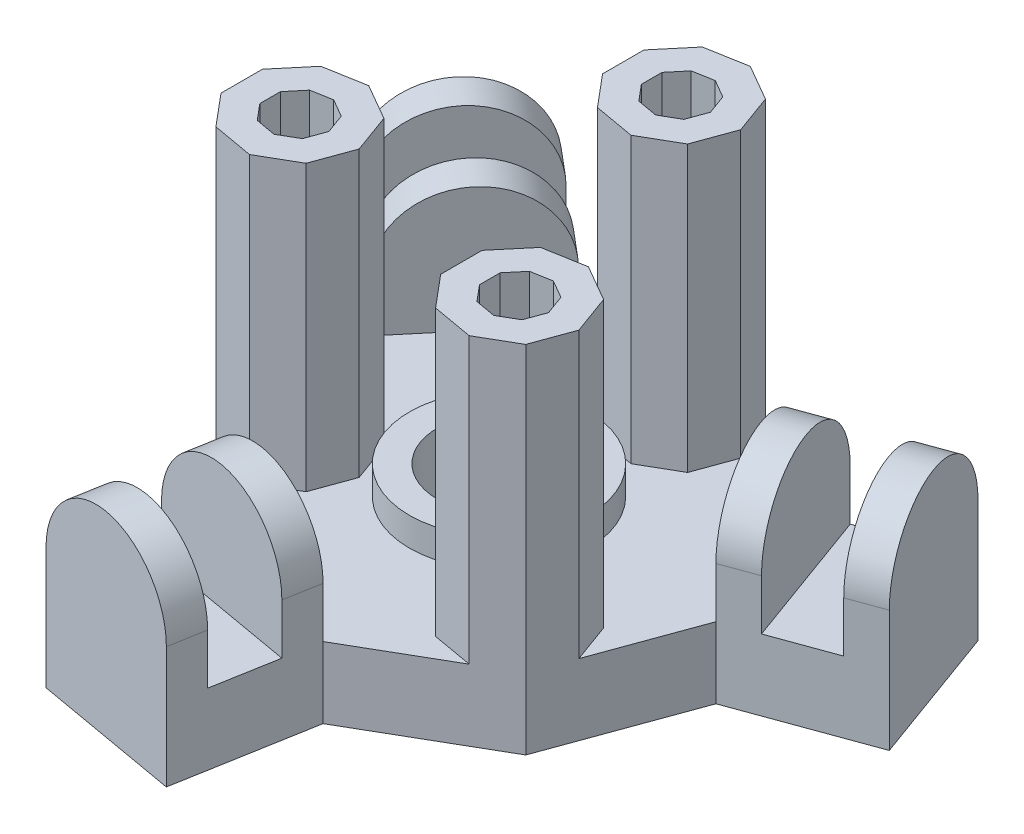
SolidWorks part; units mm, degrees
ref_plane "Front Plane" through (0, 0, 0) normal (0, 0, 1) x (1, 0, 0)
ref_plane "Top Plane" through (0, 0, 0) normal (0, 1, 0) x (1, 0, 0)
ref_plane "Right Plane" through (0, 0, 0) normal (1, 0, 0) x (0, 0, -1)
sketch "Sketch1" plane through (0, 0, 0) normal (0, 1, 0) x (1, 0, 0)
  line L0 (-18.2, -6.6243) -> (-9.684, -16.7732)
  line L1 (14.8368, -12.4495) -> (19.368, 0)
  line L2 (19.368, 0) -> (14.8368, 12.4495)
  line L3 (14.8368, 12.4495) -> (3.3632, 19.0738)
  line L4 (3.3632, 19.0738) -> (-9.684, 16.7732)
  line L5 (-9.684, 16.7732) -> (-18.2, 6.6243)
  line L6 (-18.2, 6.6243) -> (-18.2, -6.6243)
  line L7 (-9.684, -16.7732) -> (3.3632, -19.0738)
  line L8 (3.3632, -19.0738) -> (14.8368, -12.4495)
  line L9 (14.8368, 12.4495) -> (19.368, 0)
  line L10 (14.8368, 12.4495) -> (26.1868, 16.5806)
  line L11 (19.368, 0) -> (30.718, 4.1311)
  line L12 (26.1868, 16.5806) -> (30.718, 4.1311)
  line L13 (3.3632, -19.0738) -> (-9.684, -16.7732)
  line L14 (3.3632, -19.0738) -> (1.2658, -30.9687)
  line L15 (-9.684, -16.7732) -> (-11.7814, -28.6681)
  line L16 (1.2658, -30.9687) -> (-11.7814, -28.6681)
  line L17 (-18.2, 6.6243) -> (-9.684, 16.7732)
  line L18 (-18.2, 6.6243) -> (-27.4526, 14.3881)
  line L19 (-9.684, 16.7732) -> (-18.9366, 24.5371)
  line L20 (-27.4526, 14.3881) -> (-18.9366, 24.5371)
  circle A0 centre (0, 0) radius 18.2 construction
  circle A1 centre (0, 0) radius 5.5
  dimension "D1" = 36.4
  dimension "D2" = 11
  dimension "D3" = 11.35
extrude "Boss-Extrude1" add sketch "Sketch1" along normal blind 6.35 contours L16 L14 L7 L15 | L7 L8 L1 L2 L3 L4 L5 L6 L0 A1 | L12 L10 L2 L11 | L20 L18 L5 L19
ref_plane "Plane1" through (-5.2578, 0, 29.8184) normal (0.1736, 0, -0.9848) x (-0.9848, 0, -0.1736)
sketch "Sketch4" plane through (-5.2578, 0, 29.8184) normal (0.1736, 0, -0.9848) x (-0.9848, 0, -0.1736)
  line L0 (-6.6243, 6.35) -> (-6.6243, 10.85)
  line L1 (6.6243, 6.35) -> (6.6243, 10.85)
  line L2 (-6.6243, 6.35) -> (6.6243, 6.35)
  arc A0 (6.6243, 10.85) -> (-6.6243, 10.85) centre (0, 10.85) ccw
  dimension "D1" = 4.5
extrude "Boss-Extrude2" add sketch "Sketch4" along normal blind 3.18
ref_plane "Plane2" through (-3.1604, 0, 17.9235) normal (0.1736, 0, -0.9848) x (-0.9848, 0, -0.1736)
sketch "Sketch6" plane through (-3.1604, 0, 17.9235) normal (0.1736, 0, -0.9848) x (-0.9848, 0, -0.1736)
  line L0 (-6.6243, 6.35) -> (-6.6243, 10.85)
  line L1 (6.6243, 6.35) -> (6.6243, 10.85)
  line L2 (-6.6243, 6.35) -> (6.6243, 6.35)
  arc A0 (6.6243, 10.85) -> (-6.6243, 10.85) centre (0, 10.85) ccw
  dimension "D1" = 4.5
extrude "Boss-Extrude4" add sketch "Sketch6" against normal blind 3.175
ref_plane "Plane3" through (28.4524, 0, -10.3558) normal (-0.9397, 0, 0.342) x (0.342, 0, 0.9397)
sketch "Sketch8" plane through (28.4524, 0, -10.3558) normal (-0.9397, 0, 0.342) x (0.342, 0, 0.9397)
  line L0 (-6.6243, 10.85) -> (-6.6243, 6.35)
  line L1 (-6.6243, 6.35) -> (6.6243, 6.35)
  line L2 (6.6243, 6.35) -> (6.6243, 10.85)
  arc A0 (6.6243, 10.85) -> (-6.6243, 10.85) centre (0, 10.85) ccw
  dimension "D1" = 4.5
extrude "Boss-Extrude5" add sketch "Sketch8" along normal blind 3.175
ref_plane "Plane4" through (17.1024, 0, -6.2248) normal (-0.9397, 0, 0.342) x (0.342, 0, 0.9397)
sketch "Sketch9" plane through (17.1024, 0, -6.2248) normal (-0.9397, 0, 0.342) x (0.342, 0, 0.9397)
  line L0 (-6.6243, 6.35) -> (-6.6243, 10.85)
  line L1 (-6.6243, 6.35) -> (6.6243, 6.35)
  line L2 (6.6243, 6.35) -> (6.6243, 10.85)
  arc A0 (-6.6243, 10.85) -> (6.6243, 10.85) centre (0, 10.85) cw
  dimension "D1" = 4.5
extrude "Boss-Extrude6" add sketch "Sketch9" against normal blind 3.175
ref_plane "Plane5" through (-23.1946, 0, -19.4626) normal (0.766, 0, 0.6428) x (0.6428, 0, -0.766)
sketch "Sketch10" plane through (-23.1946, 0, -19.4626) normal (0.766, 0, 0.6428) x (0.6428, 0, -0.766)
  line L0 (-6.6243, 10.85) -> (-6.6243, 6.35)
  line L1 (-6.6243, 6.35) -> (6.6243, 6.35)
  line L2 (6.6243, 6.35) -> (6.6243, 10.85)
  arc A0 (6.6243, 10.85) -> (-6.6243, 10.85) centre (0, 10.85) ccw
  dimension "D1" = 4.5
extrude "Boss-Extrude7" add sketch "Sketch10" along normal blind 3.175
ref_plane "Plane6" through (-13.942, 0, -11.6987) normal (0.766, 0, 0.6428) x (0.6428, 0, -0.766)
sketch "Sketch11" plane through (-13.942, 0, -11.6987) normal (0.766, 0, 0.6428) x (0.6428, 0, -0.766)
  line L0 (-6.6243, 10.85) -> (-6.6243, 6.35)
  line L1 (-6.6243, 6.35) -> (6.6243, 6.35)
  line L2 (6.6243, 6.35) -> (6.6243, 10.85)
  arc A0 (6.6243, 10.85) -> (-6.6243, 10.85) centre (0, 10.85) ccw
  dimension "D1" = 4.5
extrude "Boss-Extrude8" add sketch "Sketch11" against normal blind 3.175
ref_plane "Plane7" through (0, 6.35, 0) normal (0, 1, 0) x (1, 0, 0)
sketch "Sketch12" plane through (0, 6.35, 0) normal (0, 1, 0) x (1, 0, 0)
  line L9 (14.8368, -12.4495) -> (19.368, 0) construction
  line L29 (14.8368, -12.4495) -> (16.1015, -8.9746)
  line L38 (16.1015, -8.9746) -> (14.8368, -5.4997)
  line L48 (6.5657, 10.275) -> (7.8305, 13.7499)
  line L49 (3.3632, 19.0738) -> (-0.2785, 18.4317)
  line L50 (-0.2785, 18.4317) -> (-2.6555, 15.5989)
  line L51 (-2.6555, 15.5989) -> (-2.6555, 11.9009)
  line L52 (-2.6555, 11.9009) -> (-0.2785, 9.0681)
  line L53 (-0.2785, 9.0681) -> (3.3632, 8.426)
  line L54 (3.3632, 8.426) -> (6.5657, 10.275)
  line L55 (7.8305, 13.7499) -> (6.5657, 17.2248)
  line L56 (6.5657, 17.2248) -> (3.3632, 19.0738)
  line L57 (14.8368, -5.4997) -> (11.6343, -3.6507)
  line L58 (11.6343, -3.6507) -> (7.9925, -4.2929)
  line L59 (7.9925, -4.2929) -> (5.6155, -7.1256)
  line L60 (5.6155, -7.1256) -> (5.6155, -10.8236)
  line L61 (5.6155, -10.8236) -> (7.9925, -13.6564)
  line L62 (7.9925, -13.6564) -> (11.6343, -14.2985)
  line L63 (11.6343, -14.2985) -> (14.8368, -12.4495)
  line L64 (-18.2, -6.6243) -> (-9.684, -16.7732) construction
  line L65 (3.3632, -19.0738) -> (14.8368, -12.4495) construction
  line L66 (-18.2, -6.6243) -> (-15.823, -9.457)
  line L67 (-15.823, -9.457) -> (-12.1813, -10.0992)
  line L68 (-12.1813, -10.0992) -> (-8.9787, -8.2502)
  line L69 (-8.9787, -8.2502) -> (-7.714, -4.7753)
  line L70 (-7.714, -4.7753) -> (-8.9787, -1.3004)
  line L71 (-8.9787, -1.3004) -> (-12.1813, 0.5486)
  line L72 (-12.1813, 0.5486) -> (-15.823, -0.0935)
  line L73 (-15.823, -0.0935) -> (-18.2, -2.9263)
  line L74 (-18.2, -2.9263) -> (-18.2, -6.6243)
  line L75 (14.8368, 12.4495) -> (3.3632, 19.0738) construction
  line L76 (-0.1155, 12.8254) -> (1.073, 11.409)
  line L77 (4.4951, 12.0124) -> (5.1275, 13.7499)
  line L78 (5.1275, 13.7499) -> (4.4951, 15.4874)
  line L79 (4.4951, 15.4874) -> (2.8939, 16.4118)
  line L80 (2.8939, 16.4118) -> (1.073, 16.0908)
  line L81 (1.073, 16.0908) -> (-0.1155, 14.6744)
  line L82 (-0.1155, 14.6744) -> (-0.1155, 12.8254)
  line L83 (1.073, 11.409) -> (2.8939, 11.088)
  line L84 (2.8939, 11.088) -> (4.4951, 12.0124)
  line L86 (12.7661, -10.7121) -> (13.3985, -8.9746)
  line L87 (13.3985, -8.9746) -> (12.7661, -7.2371)
  line L88 (12.7661, -7.2371) -> (11.1649, -6.3127)
  line L89 (11.1649, -6.3127) -> (9.344, -6.6337)
  line L90 (9.344, -6.6337) -> (8.1555, -8.0501)
  line L91 (8.1555, -8.0501) -> (8.1555, -9.8991)
  line L92 (8.1555, -9.8991) -> (9.344, -11.3155)
  line L93 (9.344, -11.3155) -> (11.1649, -11.6366)
  line L94 (11.1649, -11.6366) -> (12.7661, -10.7121)
  line L95 (-11.0494, -6.5128) -> (-10.417, -4.7753)
  line L96 (-10.417, -4.7753) -> (-11.0494, -3.0378)
  line L97 (-11.0494, -3.0378) -> (-12.6506, -2.1133)
  line L98 (-12.6506, -2.1133) -> (-14.4715, -2.4344)
  line L99 (-14.4715, -2.4344) -> (-15.66, -3.8508)
  line L100 (-15.66, -3.8508) -> (-15.66, -5.6998)
  line L101 (-15.66, -5.6998) -> (-14.4715, -7.1162)
  line L102 (-14.4715, -7.1162) -> (-12.6506, -7.4372)
  line L103 (-12.6506, -7.4372) -> (-11.0494, -6.5128)
  circle A0 centre (2.4245, 13.7499) radius 5.08 construction
  circle A1 centre (10.6955, -8.9746) radius 5.08 construction
  circle A2 centre (-13.12, -4.7753) radius 5.08 construction
  circle A3 centre (2.4245, 13.7499) radius 2.54 construction
  circle A4 centre (10.6955, -8.9746) radius 2.54 construction
  circle A5 centre (-13.12, -4.7753) radius 2.54 construction
  dimension "D1" = 10.16
  dimension "D2" = 2.54
  dimension "D3" = 2.54
  dimension "D4" = 2.54
extrude "Boss-Extrude9" add sketch "Sketch12" along normal blind 25.4
ref_plane "Plane8" through (0, 6.35, 0) normal (0, 1, 0) x (1, 0, 0)
sketch "Sketch15" plane through (0, 6.35, 0) normal (0, 1, 0) x (1, 0, 0)
  circle A0 centre (0, 0) radius 5.5
  circle A2 centre (0, 0) radius 8
  dimension "D1" = 11
  dimension "D2" = 16
extrude "Boss-Extrude10" add sketch "Sketch15" along normal blind 2.54
